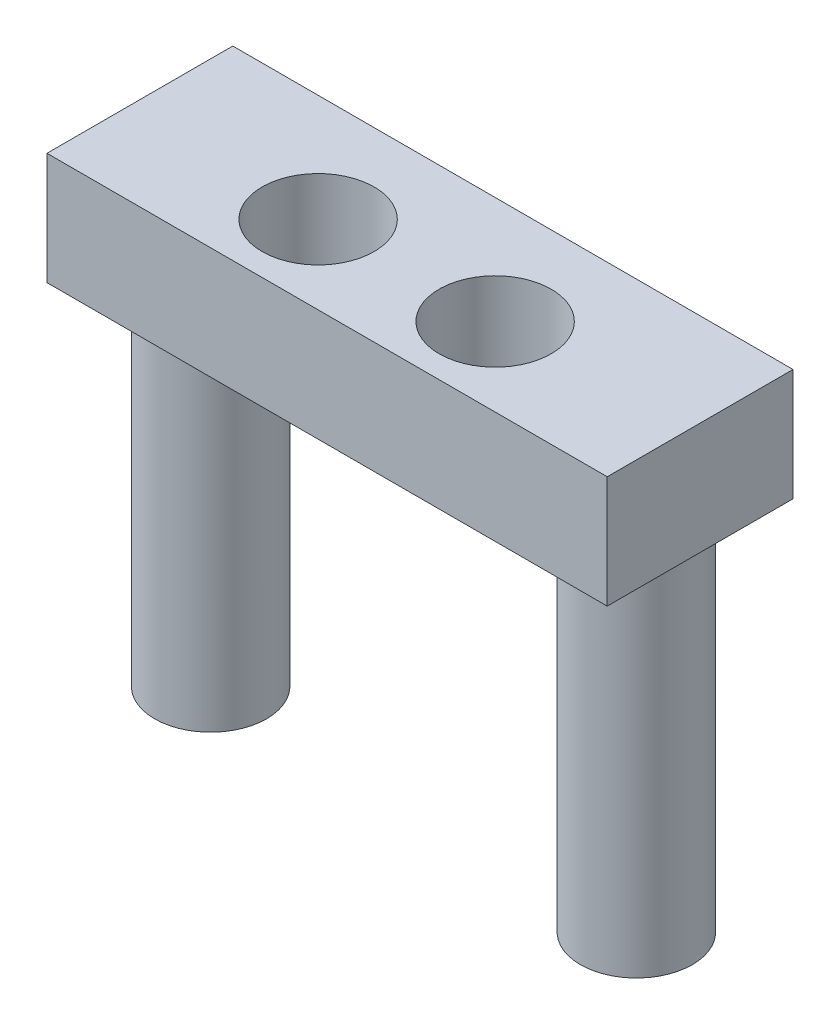
SolidWorks part; units mm, degrees
ref_plane "Front Plane" through (0, 0, 0) normal (0, 0, 1) x (1, 0, 0)
ref_plane "Top Plane" through (0, 0, 0) normal (0, 1, 0) x (1, 0, 0)
ref_plane "Right Plane" through (0, 0, 0) normal (1, 0, 0) x (0, 0, -1)
sketch "Sketch1" plane through (0, 0, 0) normal (0, 1, 0) x (1, 0, 0)
  line L1 (-15.9383, 28.9841) -> (34.0617, 28.9841)
  line L2 (-15.9383, 28.9841) -> (-15.9383, 12.4011)
  line L3 (-15.9383, 12.4011) -> (34.0617, 12.4011)
  line L4 (34.0617, 28.9841) -> (34.0617, 12.4011)
  circle A0 centre (1.2617, 19.4011) radius 5
  circle A1 centre (17.0617, 19.4011) radius 5
  circle A4 centre (17.0617, 19.4011) radius 5 construction
  circle A5 centre (1.2617, 19.4011) radius 5 construction
  dimension "D1" = 50
extrude "Boss-Extrude1" add sketch "Sketch1" along normal blind 10
sketch "Sketch2" plane through (0, 0, 0) normal (0, -1, 0) x (1, 0, 0)
  line L1 (34.0617, -12.4011) -> (34.0617, -28.9841) construction
  line L2 (-15.9383, -28.9841) -> (-15.9383, -12.4011) construction
  circle A0 centre (28.0617, -21.0042) radius 5
  circle A1 centre (-9.9383, -21.0042) radius 5
  dimension "D1" = 6
  dimension "D2" = 6
extrude "Boss-Extrude2" add sketch "Sketch2" along normal up to surface (32.5158 mm away)
sketch "Sketch3" plane through (0, -32.5158, 0) normal (0, -1, 0) x (1, 0, 0)
  circle A0 centre (28.0617, -21.0042) radius 1.75
  circle A1 centre (-9.9383, -21.0042) radius 1.75
extrude "Cut-Extrude1" cut sketch "Sketch3" against normal blind 10
